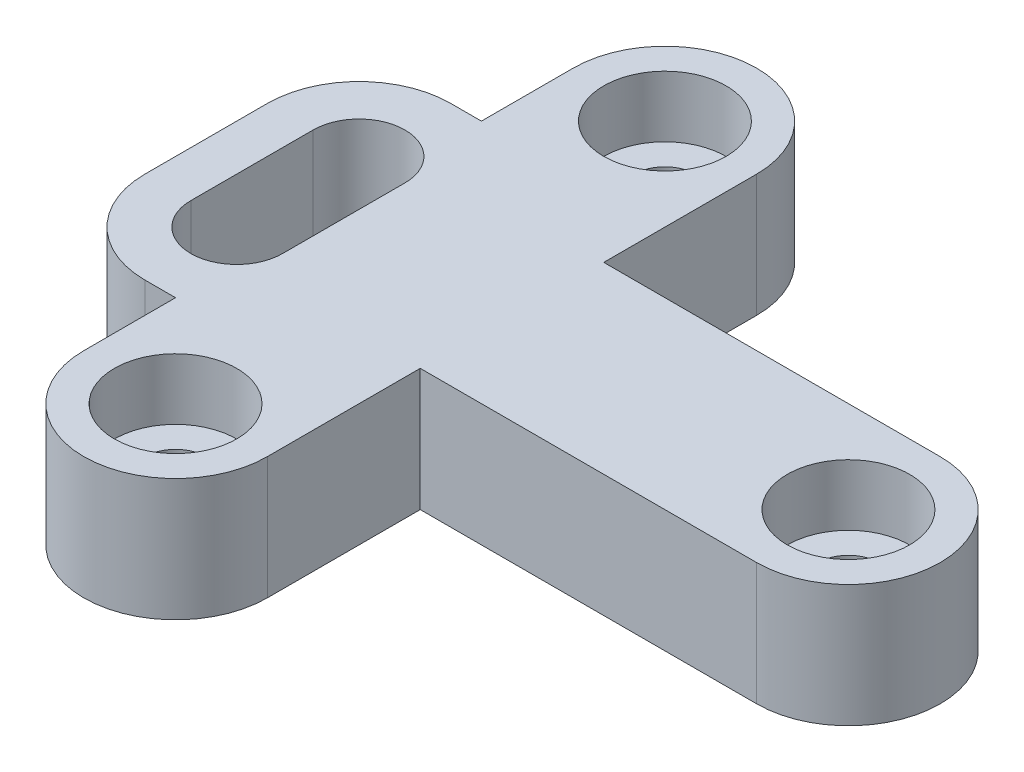
SolidWorks part; units mm, degrees
ref_plane "Front Plane" through (0, 0, 0) normal (0, 0, 1) x (1, 0, 0)
ref_plane "Top Plane" through (0, 0, 0) normal (0, 1, 0) x (1, 0, 0)
ref_plane "Right Plane" through (0, 0, 0) normal (1, 0, 0) x (0, 0, -1)
sketch "Sketch2" plane through (0, 0, 0) normal (0, 1, 0) x (1, 0, 0)
  line L0 (0, 0) -> (0, -30) construction
  line L1 (0, -30) -> (20, -30) construction
  line L4 (5, -30) -> (5, -15)
  line L5 (5, -15) -> (0, -15)
  line L6 (0, 0) -> (0, 20) construction
  line L7 (-15, 20) -> (-15, 0)
  line L8 (0, 10) -> (249.0049, 10) construction
  line L9 (5, 35) -> (0, 35)
  line L10 (5, 50) -> (5, 35)
  line L11 (90, 25) -> (35, 25) construction
  line L12 (35, 50) -> (35, 25)
  line L13 (35, 25) -> (90, 25)
  line L14 (35, -30) -> (35, -5)
  line L15 (35, -5) -> (90, -5)
  line L16 (0, 20) -> (0, 0) construction
  line L17 (7.5, 20) -> (7.5, 0)
  line L18 (-7.5, 20) -> (-7.5, 0)
  arc A0 (-15, 0) -> (0, -15) centre (0, 0) ccw
  arc A1 (5, -30) -> (35, -30) centre (20, -30) ccw
  arc A2 (0, 35) -> (-15, 20) centre (0, 20) ccw
  arc A3 (5, 50) -> (35, 50) centre (20, 50) cw
  arc A4 (90, -5) -> (90, 25) centre (90, 10) ccw
  arc A5 (7.5, 20) -> (-7.5, 20) centre (0, 20) ccw
  arc A6 (-7.5, 0) -> (7.5, 0) centre (0, 0) ccw
  point P19 (0, 10)
  dimension "D1" = 30
  dimension "D4" = 30
  dimension "D6" = 30
  dimension "D7" = 30
  dimension "D10" = 7.5
  dimension "D2" = 30
  dimension "D3" = 20
  dimension "D5" = 20
  dimension "D8" = 90
  dimension "D9" = 20
extrude "Boss-Extrude2" add sketch "Sketch2" along normal mid plane 20
sketch "Sketch3" plane through (0, 10, 0) normal (0, 1, 0) x (1, 0, 0)
  circle A0 centre (90, 10) radius 10
  circle A1 centre (20, 50) radius 10
  circle A2 centre (20, -30) radius 10
  dimension "D1" = 20
  dimension "D2" = 20
  dimension "D3" = 20
extrude "Cut-Extrude1" cut sketch "Sketch3" against normal blind 10
sketch "Sketch4" plane through (0, 10, 0) normal (0, 1, 0) x (1, 0, 0)
  circle A0 centre (20, 50) radius 5
  circle A1 centre (20, -30) radius 5
  circle A2 centre (90, 10) radius 5
  dimension "D1" = 10
  dimension "D2" = 10
  dimension "D3" = 10
extrude "Cut-Extrude2" cut sketch "Sketch4" against normal through all
